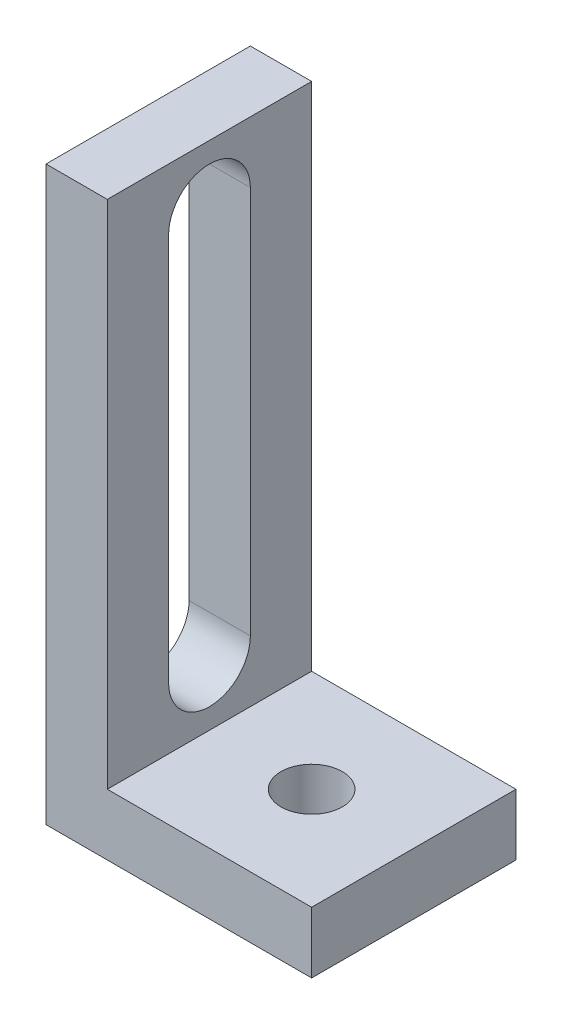
SolidWorks part; units mm, degrees
ref_plane "前视基准面" through (0, 0, 0) normal (0, 0, 1) x (1, 0, 0)
ref_plane "上视基准面" through (0, 0, 0) normal (0, 1, 0) x (1, 0, 0)
ref_plane "右视基准面" through (0, 0, 0) normal (1, 0, 0) x (0, 0, -1)
sketch "草图2" plane through (0, 0, 0) normal (0, 1, 0) x (1, 0, 0)
  line L0 (0, 0) -> (0, -10)
  line L1 (0, -10) -> (10, -10)
  line L2 (10, -10) -> (10, 0)
  line L3 (10, 0) -> (0, 0)
extrude "凸台-拉伸2" add sketch "草图2" along normal blind 3 contours L3 L0 L1 L2
sketch "草图3" plane through (0, 3, 0) normal (0, 1, 0) x (1, 0, 0)
  line L0 (0, -5) -> (10, -5) construction
  line L1 (0, 0) -> (0, -10) construction
  line L2 (10, -10) -> (10, 0) construction
  circle A0 centre (5, -5) radius 1.5
extrude "切除-拉伸1" cut sketch "草图3" against normal blind 3
sketch "草图5" plane through (0, 0, 10) normal (0, 0, 1) x (1, 0, 0)
  line L0 (0, 3) -> (0, 28)
  line L1 (0, 28) -> (-3, 28)
  line L2 (-3, 28) -> (-3, 0)
  line L3 (-3, 0) -> (0, 0)
  line L8 (0, 0) -> (10, 0)
  line L9 (10, 0) -> (10, 3)
  line L10 (10, 3) -> (0, 3)
  line L11 (0, 3) -> (0, 0)
  line L15 (0, 3) -> (0, 0)
  dimension "D1" = 0
extrude "凸台-拉伸3" add sketch "草图5" against normal through all
sketch "草图6" plane through (0, 0, 0) normal (1, 0, 0) x (0, 0, -1)
  line L0 (-5, 28) -> (-5, 3) construction
  line L1 (0, 28) -> (-10, 28) construction
  line L2 (-10, 3) -> (0, 3) construction
  line L3 (-5, 25) -> (-5, 6) construction
  line L4 (-3, 25) -> (-3, 6)
  line L5 (-7, 25) -> (-7, 6)
  arc A0 (-3, 25) -> (-7, 25) centre (-5, 25) ccw
  arc A1 (-7, 6) -> (-3, 6) centre (-5, 6) ccw
  point P6 (-5, 25)
  point P7 (-5, 6)
  point P8 (-5, 15.5)
extrude "切除-拉伸2" cut sketch "草图6" against normal blind 10
